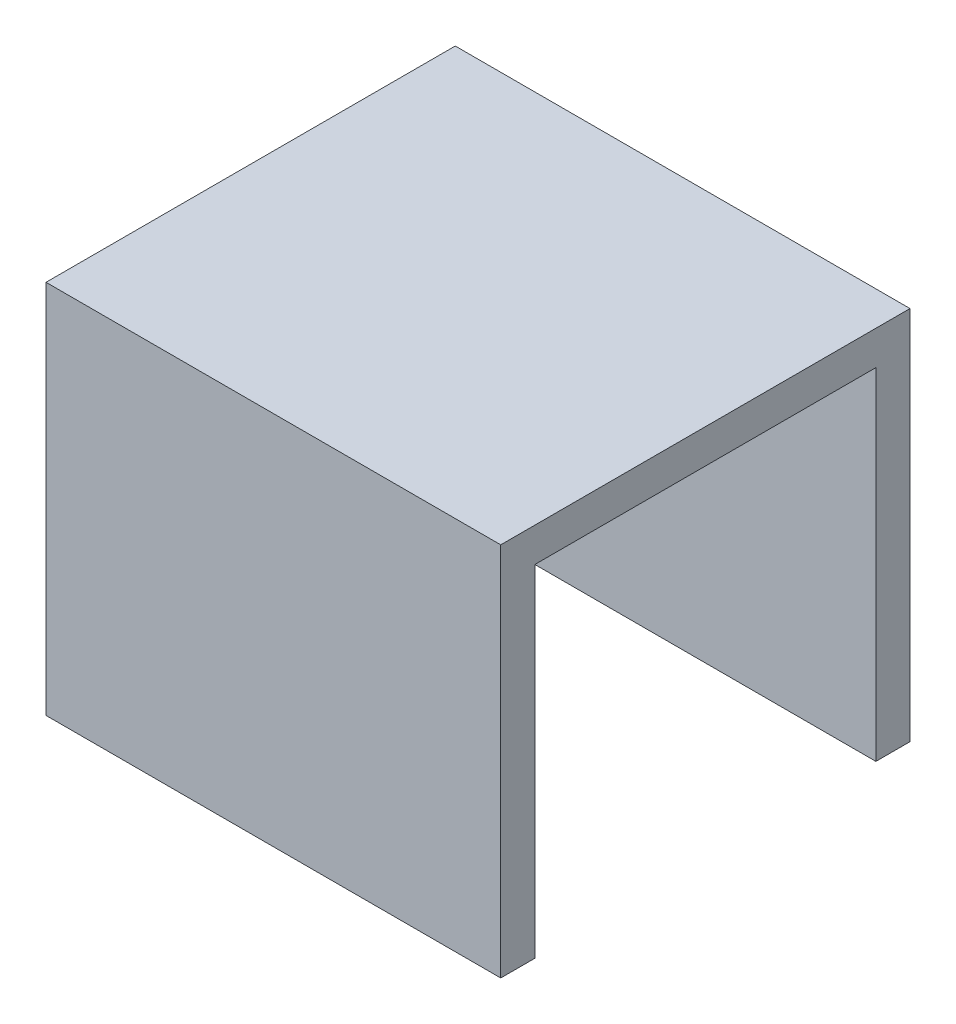
SolidWorks part; units mm, degrees
ref_plane "Front Plane" through (0, 0, 0) normal (0, 0, 1) x (1, 0, 0)
ref_plane "Top Plane" through (0, 0, 0) normal (0, 1, 0) x (1, 0, 0)
ref_plane "Right Plane" through (0, 0, 0) normal (1, 0, 0) x (0, 0, -1)
sketch "Sketch1" plane through (0, 0, 0) normal (0, 1, 0) x (1, 0, 0)
  line L1 (10, -9) -> (-10, -9)
  line L2 (10, -9) -> (10, 9)
  line L3 (10, 9) -> (-10, 9)
  line L4 (-10, -9) -> (-10, 9)
  line L5 (10, -9) -> (-10, 9) construction
  line L6 (10, 9) -> (-10, -9) construction
  point P0 (0, 0)
  dimension "D1" = 18
  dimension "D2" = 20
extrude "Boss-Extrude1" add sketch "Sketch1" along normal blind 16.5
sketch "Sketch2" plane through (-10, 0, 0) normal (-1, 0, 0) x (0, 0, 1)
  line L0 (-9, 0) -> (9, 0) construction
  line L1 (-7.5, 0) -> (7.5, 0)
  line L2 (-7.5, 0) -> (-7.5, 15)
  line L3 (-7.5, 15) -> (7.5, 15)
  line L4 (7.5, 0) -> (7.5, 15)
  line L5 (-7.5, 0) -> (-9, 0) construction
  line L6 (7.5, 0) -> (9, 0) construction
  dimension "D1" = 15
  dimension "D2" = 15
extrude "Cut-Extrude1" cut sketch "Sketch2" against normal up to next
